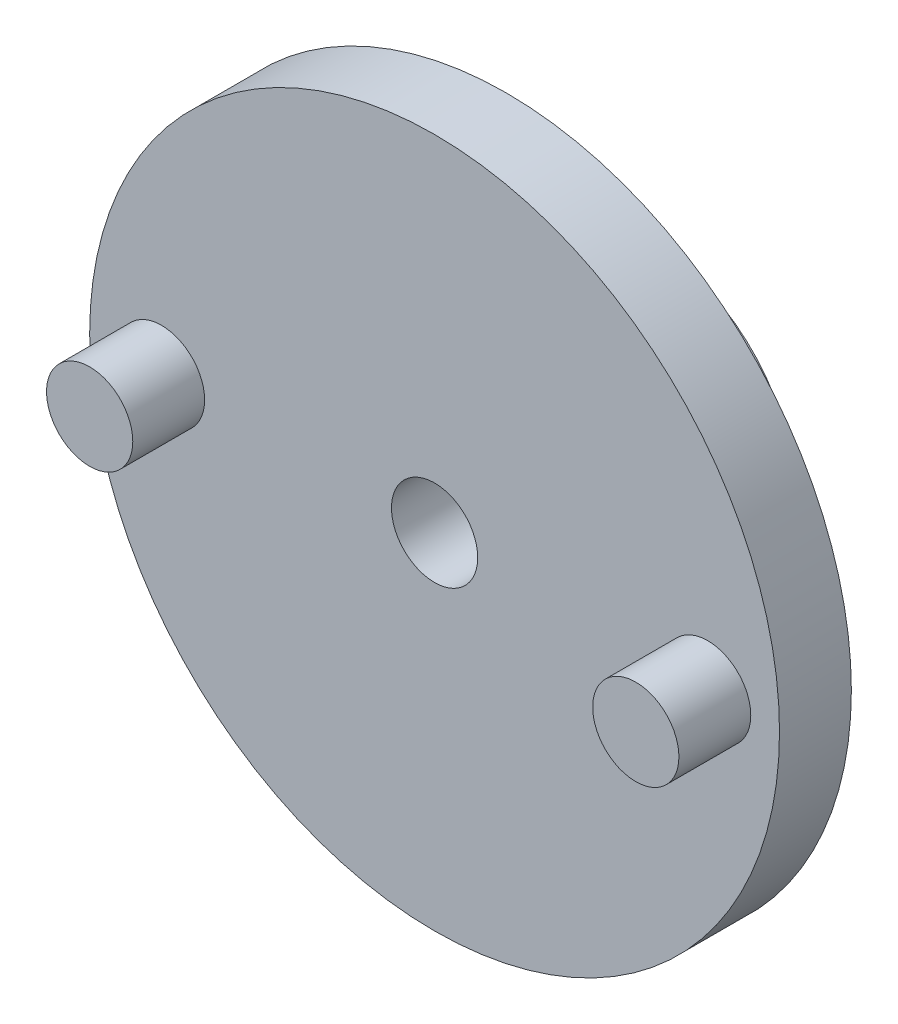
SolidWorks part; units mm, degrees
ref_plane "Alzado" through (0, 0, 0) normal (0, 0, 1) x (1, 0, 0)
ref_plane "Planta" through (0, 0, 0) normal (0, 1, 0) x (1, 0, 0)
ref_plane "Vista lateral" through (0, 0, 0) normal (1, 0, 0) x (0, 0, -1)
sketch "Croquis1" plane through (0, 0, 0) normal (0, 0, 1) x (1, 0, 0)
  circle A0 centre (0, 0) radius 12
  dimension "D1" = 24
extrude "Saliente-Extruir1" add sketch "Croquis1" along normal blind 2.5
sketch "Croquis2" plane through (0, 0, 0) normal (0, 0, -1) x (-1, 0, 0)
  circle A0 centre (0, 0) radius 5
  dimension "D1" = 10
extrude "Saliente-Extruir2" add sketch "Croquis2" along normal blind 5
sketch "Croquis3" plane through (0, 0, -5) normal (0, 0, -1) x (-1, 0, 0)
  circle A0 centre (0, 0) radius 3.1
  dimension "D1" = 6.2
extrude "Cortar-Extruir1" cut sketch "Croquis3" against normal blind 4.2
sketch "Croquis4" plane through (0, 0, 2.5) normal (0, 0, 1) x (1, 0, 0)
  circle A0 centre (0, 0) radius 1.5
  dimension "D1" = 3
extrude "Cortar-Extruir2" cut sketch "Croquis4" against normal blind 4
sketch "Croquis5" plane through (0, 0, 2.5) normal (0, 0, 1) x (1, 0, 0)
  circle A0 centre (9.5, 0) radius 1.5
  circle A1 centre (-9.5, 0) radius 1.5
  circle A2 centre (0, 0) radius 1.5 construction
  dimension "D2" = 9.5
  dimension "D3" = 9.5
  dimension "D1" = 3
extrude "Saliente-Extruir3" add sketch "Croquis5" along normal blind 2.5
sketch "Croquis6" plane through (0, 0, 0) normal (0, 0, -1) x (-1, 0, 0)
  circle A0 centre (-9.5, 0) radius 0.75
  circle A1 centre (9.5, 0) radius 0.75
  dimension "D1" = 1.5
extrude "Cortar-Extruir3" cut sketch "Croquis6" against normal blind 2
